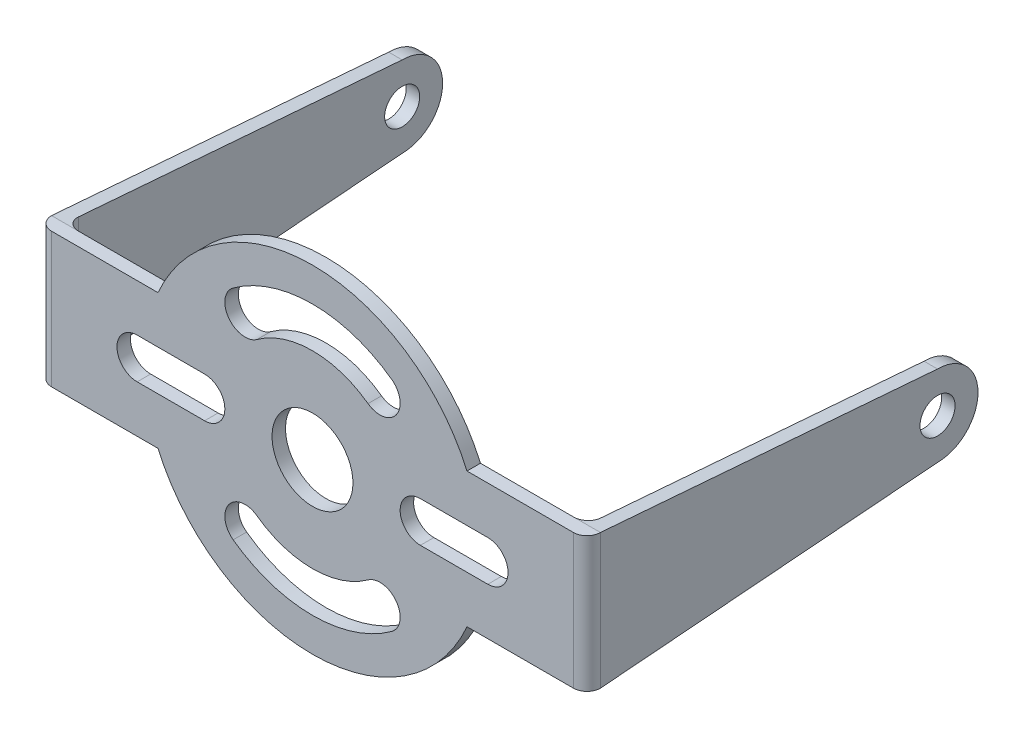
SolidWorks part; units mm, degrees
ref_plane "前视基准面" through (0, 0, 0) normal (0, 0, 1) x (1, 0, 0)
ref_plane "上视基准面" through (0, 0, 0) normal (0, 1, 0) x (1, 0, 0)
ref_plane "右视基准面" through (0, 0, 0) normal (1, 0, 0) x (0, 0, -1)
sketch "Sketch1" plane through (0, 0, 0) normal (0, 0, 1) x (1, 0, 0)
  line L1 (-20.35, 5) -> (20.35, 5)
  line L2 (-20.35, 5) -> (-20.35, -5)
  line L3 (-20.35, -5) -> (20.35, -5)
  line L4 (20.35, 5) -> (20.35, -5)
  line L5 (-20.35, 5) -> (20.35, -5) construction
  line L6 (-20.35, -5) -> (20.35, 5) construction
  circle A0 centre (0, 0) radius 12.5
  circle A1 centre (0, 0) radius 3
  dimension "D1" = 25
  dimension "D2" = 6
  dimension "D3" = 10
  dimension "D4" = 40.7
extrude "Boss-Extrude1" add sketch "Sketch1" along normal blind 1 contours L1 A0 | L1 A0 L3 A1 | A0 L3 L4 L1 | A0 L1 L2 L3 | L3 A0
sketch "Sketch2" plane through (-20.35, 0, 0) normal (-1, 0, 0) x (0, 0, 1)
  line L0 (1, 0) -> (-25, 0) construction
  line L1 (1, 5) -> (1, -5) construction
  line L2 (0, -5) -> (-25, -3)
  line L3 (-25, -3) -> (-25, 3)
  line L4 (-25, 3) -> (0, 5)
  line L5 (0, 5) -> (0, -5)
  circle A0 centre (-25, 0) radius 3
  circle A1 centre (-25, 0) radius 1.3
  line M5 (0, 5) -> (0, -5)
  dimension "D1" = 6
  dimension "D2" = 26
  dimension "D3" = 2.6
extrude "Boss-Extrude2" add sketch "Sketch2" against normal blind 1 contours L5 L0 A0 L2 | L0 L4 A0 M5 | A1 L3 A0 | A0 L0 A1 L3 | L0 A0 L3 A1
ref_plane "Plane1" through (0, 0, 0) normal (-1, 0, 0) x (0, 0, 1)
mirror "Mirror1" about plane through (0, 0, 0) normal (-1, 0, 0) of "Boss-Extrude2"
fillet "Fillet1" radius 1 4 edges at (20.35, 0, 1) (-20.35, 0, 1) (19.35, 0, 0) (-19.35, 0, 0)
sketch "Sketch3" plane through (0, 0, 1) normal (0, 0, 1) x (1, 0, 0)
  line L0 (0, 0) -> (10.5, 0) construction
  line L1 (8, 0) -> (13, 0) construction
  line L2 (8, 1.5) -> (13, 1.5)
  line L3 (8, -1.5) -> (13, -1.5)
  line L4 (0, 0) -> (0, 12.5) construction
  line L5 (-8, 0) -> (-13, 0) construction
  line L6 (-8, 1.5) -> (-13, 1.5)
  line L7 (-8, -1.5) -> (-13, -1.5)
  line L8 (6.5, 0) -> (6.5, -10.6771) construction
  arc A0 (8, 1.5) -> (8, -1.5) centre (8, 0) ccw
  arc A1 (13, -1.5) -> (13, 1.5) centre (13, 0) ccw
  arc A2 (11.4564, 5) -> (-11.4564, 5) centre (0, 0) ccw construction
  arc A3 (-8, 1.5) -> (-8, -1.5) centre (-8, 0) cw
  arc A4 (-13, -1.5) -> (-13, 1.5) centre (-13, 0) cw
  circle A5 centre (0, 0) radius 10
  circle A6 centre (0, 0) radius 7
  arc A7 (-11.4564, -5) -> (11.4564, -5) centre (0, 0) ccw construction
  circle A8 centre (0, 0) radius 8.5
  circle A9 centre (5, -6.8739) radius 1.5
  circle A10 centre (-5, -6.8739) radius 1.5
  circle A11 centre (-5, 6.8739) radius 1.5
  circle A12 centre (5, 6.8739) radius 1.5
  point P5 (10.5, 0)
  point P17 (-10.5, 0)
  dimension "D1" = 13
  dimension "D4" = 20
  dimension "D5" = 3
  dimension "D6" = 1.5
  dimension "D7" = 3
  dimension "D2" = 8
  dimension "D3" = 3
extrude "Cut-Extrude1" cut sketch "Sketch3" against normal blind 1 contours A3 A6 | L6 A8 L7 A3 A6 | A8 L6 A5 L7 | A5 L6 A4 L7 | A0 A6 | L3 A8 L2 A0 A6 | A8 L3 A5 L2 | A5 L3 A1 L2 | A8 A9 | A8 A9 | A8 A10 A5 A9 | A6 A10 A8 A9 | A10 A8 | A10 A8 | A12 A8 | A12 A8 | A8 A12 A5 A11 | A6 A12 A8 A11 | A8 A11 | A8 A11
